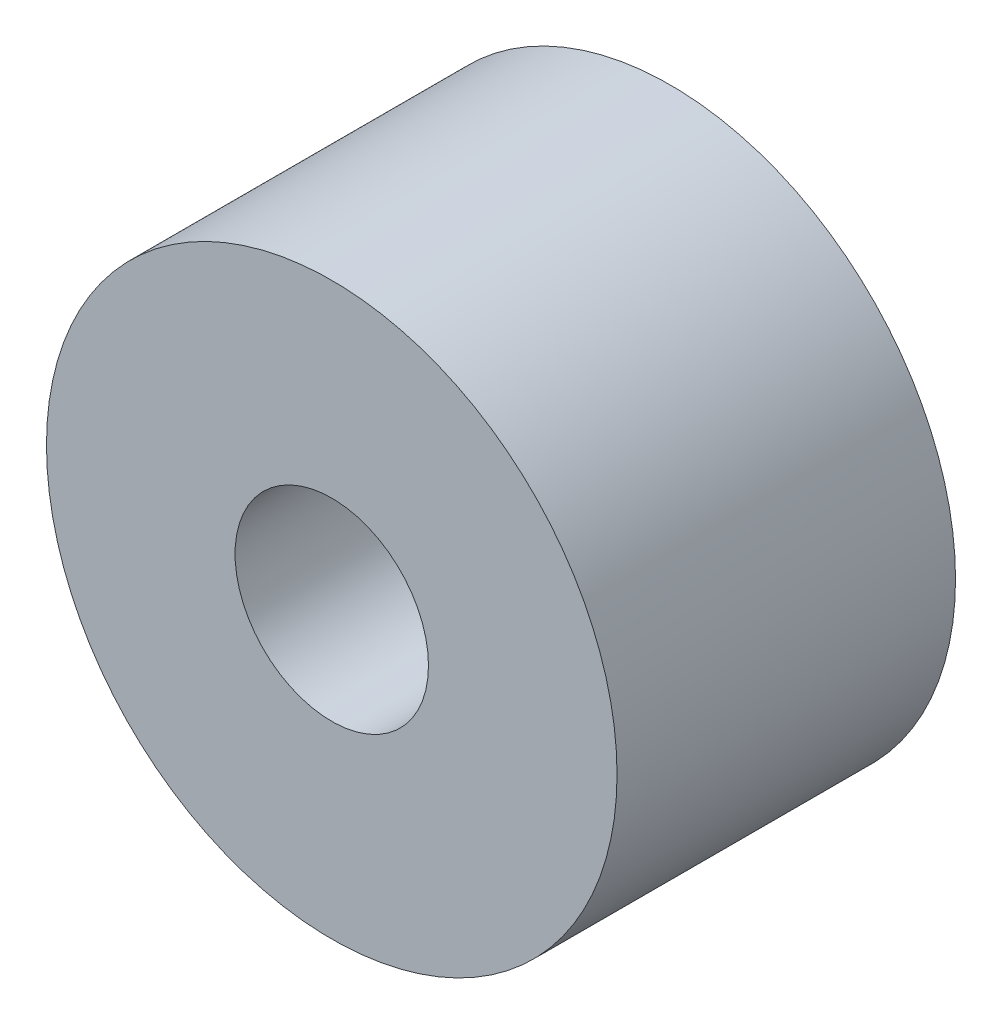
SolidWorks part; units mm, degrees
ref_plane "前视基准面" through (0, 0, 0) normal (0, 0, 1) x (1, 0, 0)
ref_plane "上视基准面" through (0, 0, 0) normal (0, 1, 0) x (1, 0, 0)
ref_plane "右视基准面" through (0, 0, 0) normal (1, 0, 0) x (0, 0, -1)
sketch "草图1" plane through (0, 0, 0) normal (0, 0, 1) x (1, 0, 0)
  circle A0 centre (0, 0) radius 5.9
  dimension "D1" = 11.8
extrude "拉伸-薄壁1" add sketch "草图1" along normal blind 7 thin thin type one direction reverse wall 3.9
